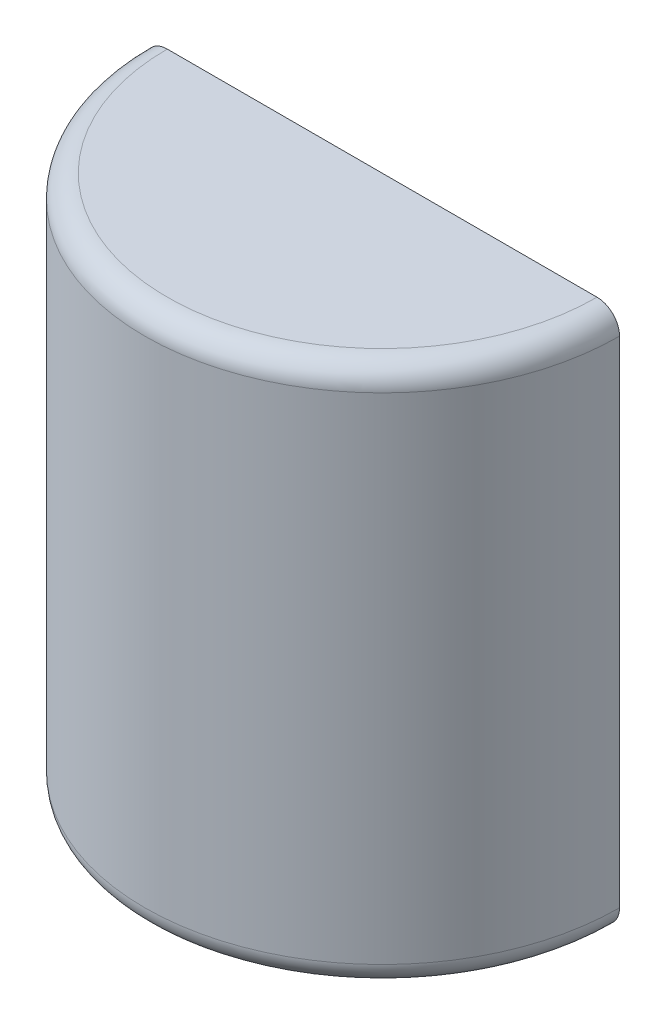
SolidWorks part; units mm, degrees
material "Custom Plastic"
ref_plane "Front Plane" through (0, 0, 0) normal (0, 0, 1) x (1, 0, 0)
ref_plane "Top Plane" through (0, 0, 0) normal (0, 1, 0) x (1, 0, 0)
ref_plane "Right Plane" through (0, 0, 0) normal (1, 0, 0) x (0, 0, -1)
sketch "Sketch1" plane through (0, 0, 0) normal (0, 0, 1) x (1, 0, 0)
  line L0 (0, 0) -> (0, 304.8) construction
  line L2 (0, 0) -> (-133.985, 0)
  line L3 (0, 0) -> (0, 304.8)
  line L4 (0, 304.8) -> (-133.985, 304.8)
  line L5 (-133.985, 0) -> (-133.985, 304.8)
  dimension "D1" = 304.8
  dimension "D2" = 133.985
revolve "Revolve1" add sketch "Sketch1" angle 180 about L0
fillet "Fillet1" radius 12.7 2 edges at (0, 0, 133.985) (0, 304.8, 133.985)
